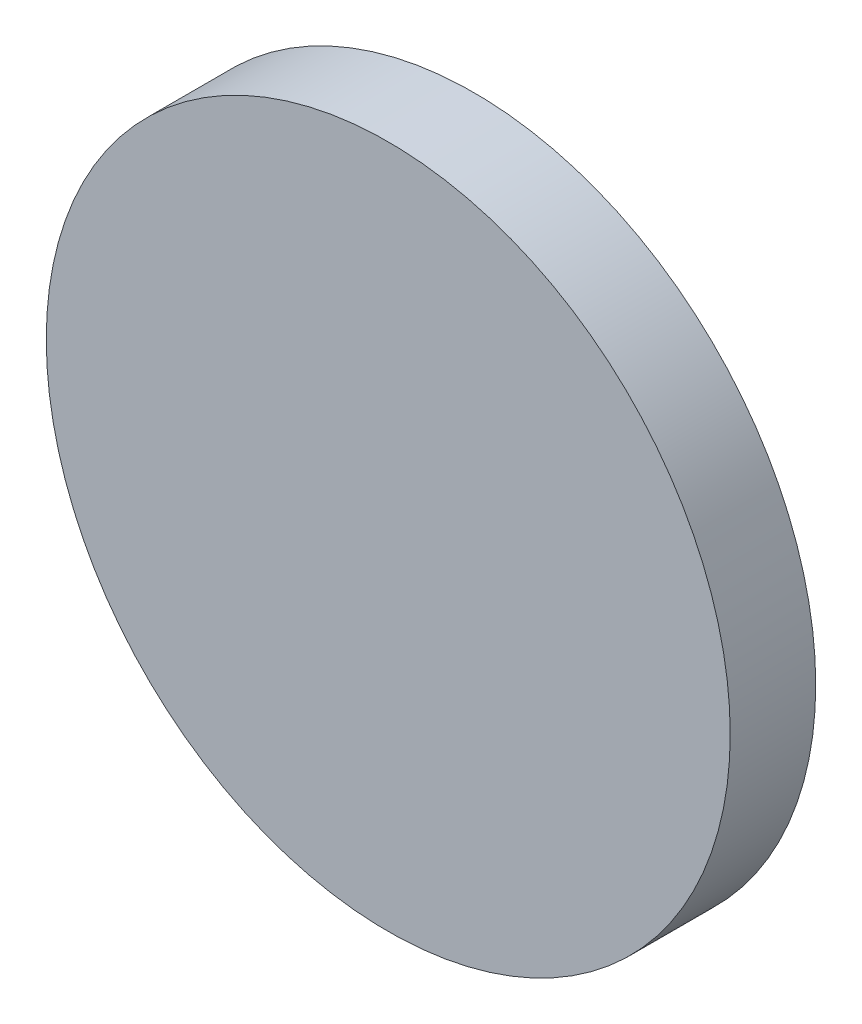
SolidWorks part; units mm, degrees
ref_plane "前视基准面" through (0, 0, 0) normal (0, 0, 1) x (1, 0, 0)
ref_plane "上视基准面" through (0, 0, 0) normal (0, 1, 0) x (1, 0, 0)
ref_plane "右视基准面" through (0, 0, 0) normal (1, 0, 0) x (0, 0, -1)
sketch "草图1" plane through (0, 0, 0) normal (0, 0, 1) x (1, 0, 0)
  circle A0 centre (0, 0) radius 20
  dimension "D1" = 40
extrude "凸台-拉伸1" add sketch "草图1" along normal blind 5 contours A0
